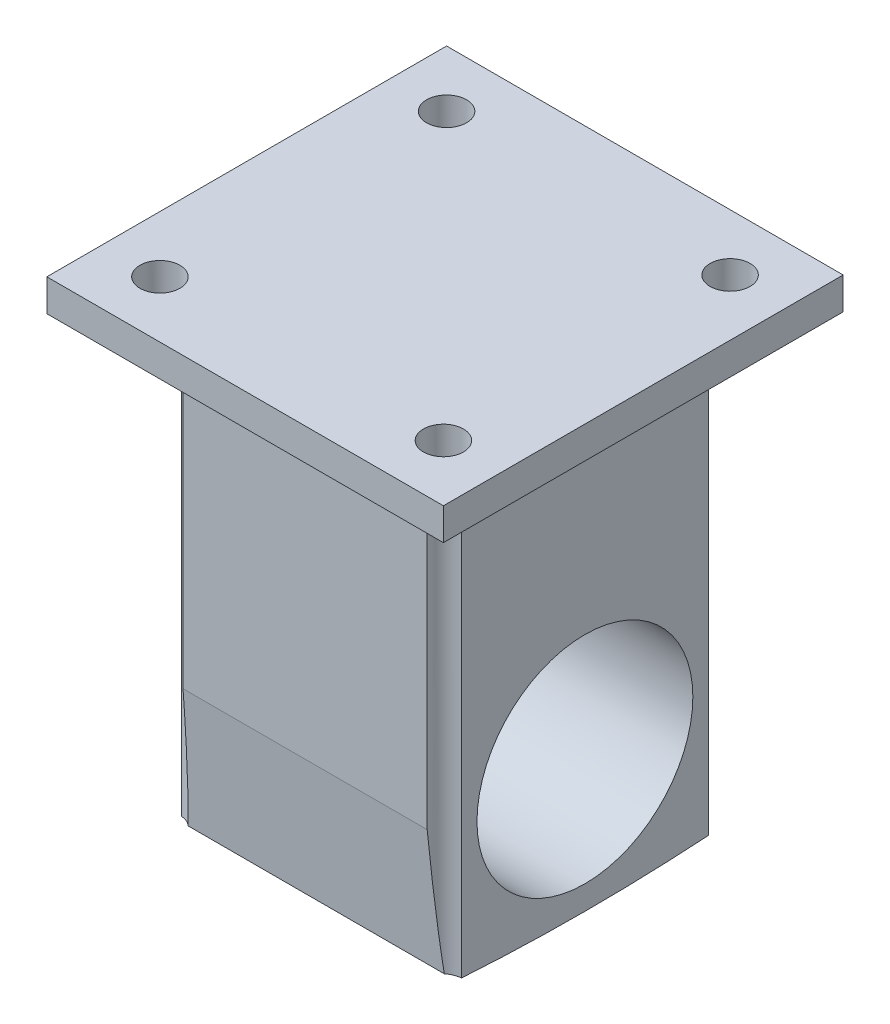
SolidWorks part; units mm, degrees
material "ABS"
ref_plane "Front Plane" through (0, 0, 0) normal (0, 0, 1) x (1, 0, 0)
ref_plane "Top Plane" through (0, 0, 0) normal (0, 1, 0) x (1, 0, 0)
ref_plane "Right Plane" through (0, 0, 0) normal (1, 0, 0) x (0, 0, -1)
sketch "Sketch1" plane through (0, 0, 0) normal (0, 1, 0) x (1, 0, 0)
  line L1 (-22.225, -22.225) -> (22.225, -22.225)
  line L2 (-22.225, -22.225) -> (-22.225, 22.225)
  line L3 (-22.225, 22.225) -> (22.225, 22.225)
  line L4 (22.225, -22.225) -> (22.225, 22.225)
  line L5 (-22.225, -22.225) -> (22.225, 22.225) construction
  line L6 (-22.225, 22.225) -> (22.225, -22.225) construction
  point P0 (0, 0)
extrude "Boss-Extrude1" add sketch "Sketch1" along normal blind 50.292
sketch "Sketch2" plane through (22.225, 0, 0) normal (1, 0, 0) x (0, 0, -1)
  line L0 (-22.225, 0) -> (-20.454, -20.2427)
  line L1 (22.225, 0) -> (20.454, -20.2427)
  line L2 (-22.225, 0) -> (22.225, 0)
  line L3 (-22.225, 0) -> (22.225, 0) construction
  arc A1 (20.454, -20.2427) -> (-20.454, -20.2427) centre (0, 279.0472) cw
  dimension "D1" = 20.32
  dimension "D2" = 20.32
  dimension "D3" = 85
  dimension "D4" = 85
extrude "Boss-Extrude2" add sketch "Sketch2" against normal up to vertex (44.45 mm away) contours L0 A1 L1 L2 up to point (-22.225, 0, -22.225)
sketch "Sketch3" plane through (22.225, 0, 0) normal (1, 0, 0) x (0, 0, -1)
  circle A0 centre (0, 0) radius 17.145
extrude "Cut-Extrude1" cut sketch "Sketch3" against normal blind 127 contours A0
sketch "Sketch4" plane through (0, 50.292, 0) normal (0, 1, 0) x (1, 0, 0)
  line L0 (31.496, -31.75) -> (-34.7458, 35.026) construction
  line L5 (31.496, -31.75) -> (-31.496, -31.75)
  line L14 (31.496, -31.75) -> (31.496, 31.75)
  line L15 (31.496, 31.75) -> (-31.496, 31.75)
  line L16 (-31.496, -31.75) -> (-31.496, 31.75)
  line L17 (31.496, -31.75) -> (-31.496, 31.75) construction
  line L18 (31.496, 31.75) -> (-31.496, -31.75) construction
  line L19 (34.7458, 35.026) -> (-31.496, -31.75) construction
  point P0 (0, 0)
  point P7 (0, 0)
  point P8 (0, 0)
  point P10 (0, 0)
extrude "Boss-Extrude3" add sketch "Sketch4" along normal blind 5.08
sketch "Sketch5" plane through (0, 55.372, 0) normal (0, 1, 0) x (1, 0, 0)
  line L0 (31.496, 31.75) -> (-31.496, 31.75) construction
  line L1 (-31.496, -31.75) -> (31.496, -31.75) construction
  line L2 (-22.5157, 22.7697) -> (-31.496, 31.75) construction
  line L3 (22.5157, 22.7697) -> (31.496, 31.75) construction
  line L4 (22.5157, -22.7697) -> (31.496, -31.75) construction
  line L5 (-22.5157, -22.7697) -> (-31.496, -31.75) construction
  line L9 (-31.496, 31.75) -> (-31.496, -31.75) construction
  line L10 (31.496, -31.75) -> (31.496, 31.75) construction
  circle A0 centre (-22.5157, 22.7697) radius 3.175
  circle A1 centre (22.5157, 22.7697) radius 3.175
  circle A2 centre (-22.5157, -22.7697) radius 3.175
  circle A3 centre (22.5157, -22.7697) radius 3.175
  point P18 (0, 0)
  point P19 (0, 0)
  point P20 (0, 0)
  dimension "D2" = 6.35
  dimension "D4" = 6.35
  dimension "D11" = 6.35
  dimension "D12" = 6.35
  dimension "D1" = 12.7
  dimension "D3" = 45
  dimension "D5" = 12.7
  dimension "D6" = 45
  dimension "D7" = 12.7
  dimension "D8" = 45
  dimension "D9" = 12.7
  dimension "D10" = 45
  dimension "D13" = 0
  dimension "D14" = 0
extrude "Cut-Extrude2" cut sketch "Sketch5" against normal through all
